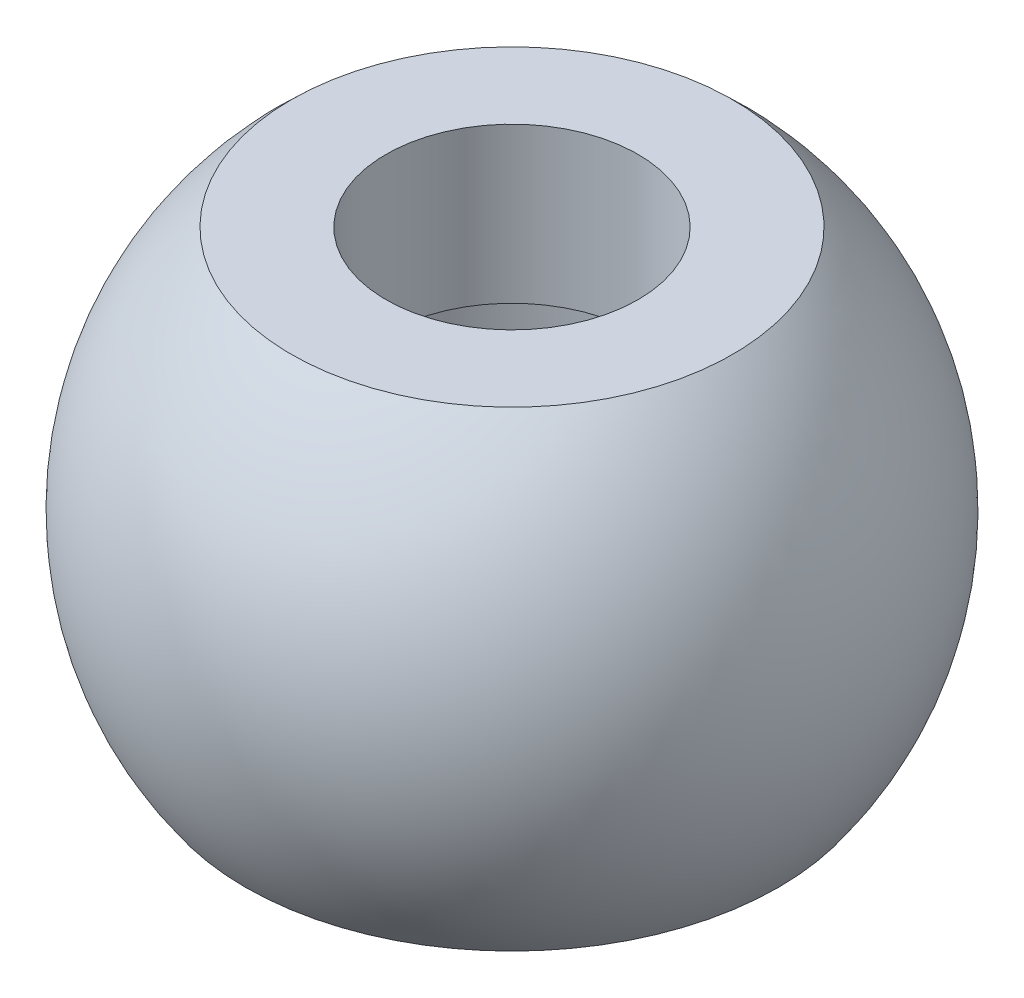
SolidWorks part; units mm, degrees
ref_plane "Front Plane" through (0, 0, 0) normal (0, 0, 1) x (1, 0, 0)
ref_plane "Top Plane" through (0, 0, 0) normal (0, 1, 0) x (1, 0, 0)
ref_plane "Right Plane" through (0, 0, 0) normal (1, 0, 0) x (0, 0, -1)
sketch "Sketch1" plane through (0, 0, 0) normal (0, 0, 1) x (1, 0, 0)
  line L0 (-13.843, 0) -> (13.843, 0) construction
  line L1 (13.843, 0) -> (16.1025, 59.0843) construction
  line L2 (-13.843, 0) -> (-16.1838, 61.2104) construction
  line L3 (-14.4562, 16.0358) -> (14.4562, 16.0358)
  line L4 (0, 0) -> (0, 39.747) construction
  line L5 (0, 16.0358) -> (0, 8.4158) construction
  line L6 (-8.255, 8.4158) -> (8.255, 8.4158)
  line L7 (-8.255, 8.4158) -> (-8.255, 16.0358)
  line L8 (8.255, 8.4158) -> (8.255, 16.0358)
  line L9 (-7.62, 0) -> (7.62, 0) construction
  line L10 (11.43, 8.4158) -> (11.43, -12.7)
  line L11 (11.43, -12.7) -> (17.4596, -12.7)
  line L12 (-11.43, -12.7) -> (-17.4596, -12.7)
  line L14 (0, 8.4158) -> (0, 2.8278) construction
  line L15 (-5.08, 2.8278) -> (5.08, 2.8278) construction
  line L16 (-5.08, 2.8278) -> (-5.08, 5.8758) construction
  line L17 (-5.08, 5.8758) -> (5.08, 5.8758) construction
  line L18 (5.08, 5.8758) -> (5.08, 2.8775) construction
  line L19 (-11.43, 8.4158) -> (11.43, 8.4158)
  line L20 (-11.43, 8.4158) -> (-11.43, -12.7)
  circle A0 centre (0, 0) radius 21.59
  point P7 (0, 0)
  point P16 (0, 8.4158)
  point P21 (0, 0)
  point P29 (0, 2.8278)
  point P41 (0, 8.4158)
  dimension "D1" = 43.18
  dimension "D2" = 27.686
  dimension "D3" = 92.19
  dimension "D4" = 92.19
  dimension "D5" = 7.62
  dimension "D6" = 16.51
  dimension "D7" = 15.24
  dimension "D8" = 6.0296
  dimension "D9" = 6.0296
  dimension "D10" = 5.588
  dimension "D11" = 10.16
  dimension "D12" = 3.048
  dimension "D13" = 22.86
revolve "Revolve1" add sketch "Sketch1" angle 360 about L4
sketch "Sketch3" plane through (0, 8.4158, 0) normal (0, -1, 0) x (1, 0, 0)
  circle A0 centre (0, 0) radius 8.255
  circle A1 centre (0, 0) radius 11.43
  circle A2 centre (0, 0) radius 14.4562 construction
  point P2 (0, 0)
  dimension "D1" = 22.86
  dimension "D2" = 16.51
extrude "Boss-Extrude3" add sketch "Sketch3" along normal blind 2.54 separate body
